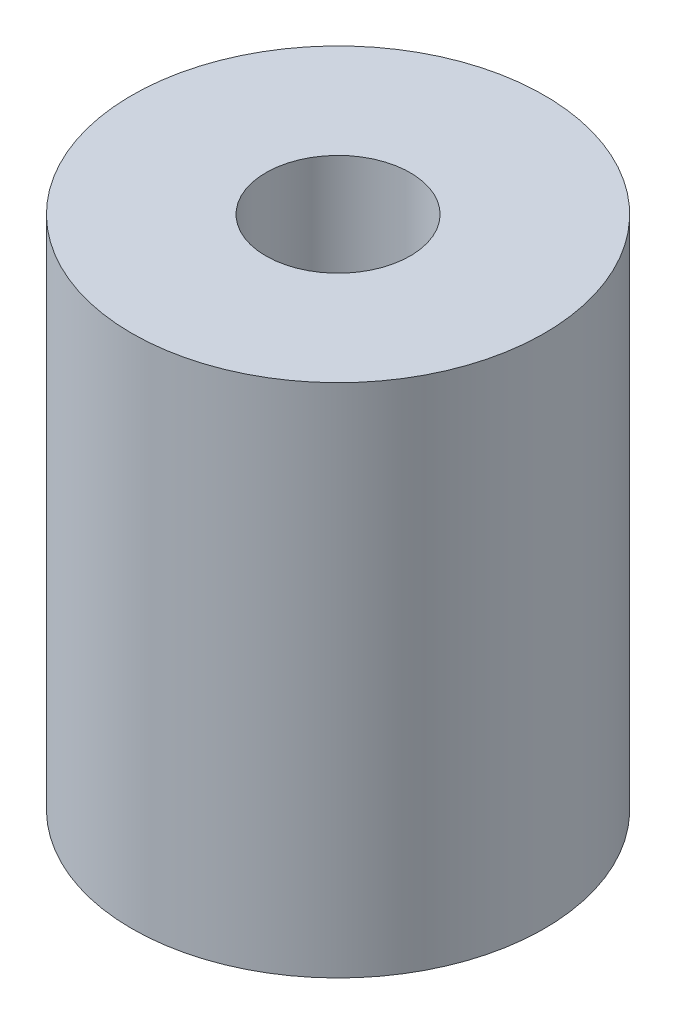
SolidWorks part; units mm, degrees
ref_plane "Front Plane" through (0, 0, 0) normal (0, 0, 1) x (1, 0, 0)
ref_plane "Top Plane" through (0, 0, 0) normal (0, 1, 0) x (1, 0, 0)
ref_plane "Right Plane" through (0, 0, 0) normal (1, 0, 0) x (0, 0, -1)
sketch "Sketch1" plane through (0, 0, 0) normal (0, 1, 0) x (1, 0, 0)
  circle A0 centre (0, 0) radius 5.08
  circle A1 centre (0, 0) radius 1.778
  dimension "D1" = 3.556
  dimension "D2" = 10.16
extrude "Boss-Extrude1" add sketch "Sketch1" along normal blind 12.7 contours A1 | A0
